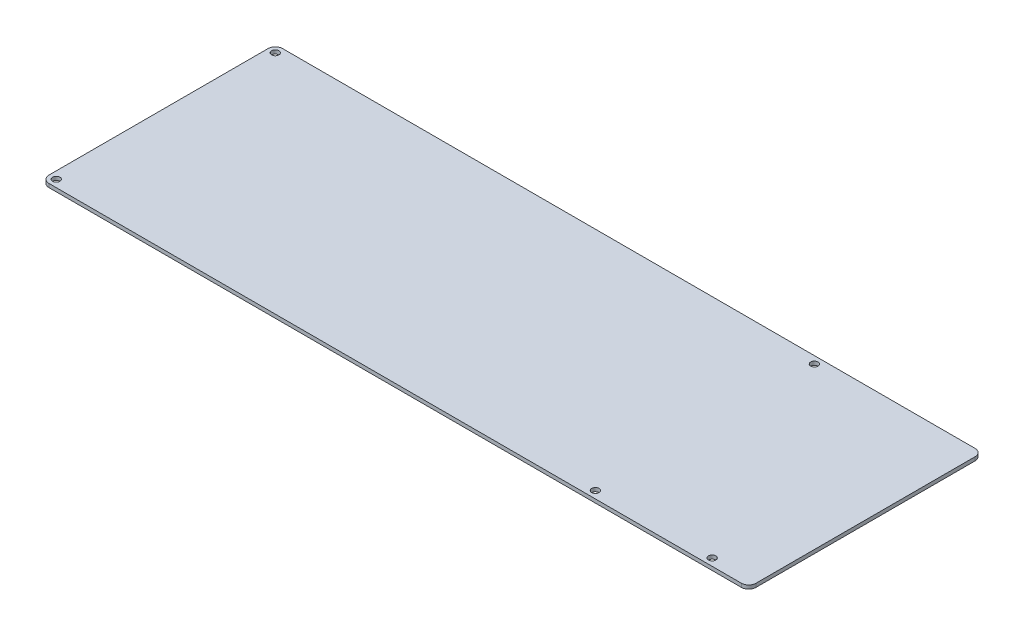
SolidWorks part; units mm, degrees
material "Delrin 2700 NC010, Low Viscosity Acetal Copolymer (SS)"
ref_plane "Front" through (0, 0, 0) normal (0, 0, 1) x (1, 0, 0)
ref_plane "Top" through (0, 0, 0) normal (0, 1, 0) x (1, 0, 0)
ref_plane "Right" through (0, 0, 0) normal (1, 0, 0) x (0, 0, -1)
sketch "Sketch1" plane through (0, 0, 0) normal (0, 1, 0) x (1, 0, 0)
  line L0 (-641.8801, 168.4566) -> (-641.8801, 78.4566) construction
  line L1 (-654.5801, 65.7566) -> (-39.6101, 65.7566)
  line L2 (-654.5801, 65.7566) -> (-654.5801, 268.9566)
  line L3 (-654.5801, 268.9566) -> (-39.6101, 268.9566)
  line L4 (-39.6101, 65.7566) -> (-39.6101, 268.9566)
  line L5 (-641.8801, 78.4566) -> (-541.8801, 78.4566) construction
  line L6 (-377.4301, 256.2566) -> (-192.0101, 256.2566) construction
  line L7 (-52.3101, 97.5066) -> (-52.3101, 237.2066) construction
  line L8 (-648.2301, 262.6066) -> (-45.9601, 262.6066) construction
  line L9 (-45.9601, 72.1066) -> (-45.9601, 262.6066) construction
  line L10 (-648.2301, 72.1066) -> (-45.9601, 72.1066) construction
  line L11 (-648.2301, 72.1066) -> (-648.2301, 262.6066) construction
  line L12 (-179.3101, 268.9566) -> (-179.3101, 65.7566) construction
  line L13 (-141.2101, 237.2066) -> (-141.2101, 97.5066) construction
  circle A0 centre (-648.2301, 262.6066) radius 3.175
  circle A1 centre (-648.2301, 72.1066) radius 3.175
  circle A2 centre (-45.9601, 262.6066) radius 3.175
  circle A3 centre (-45.9601, 72.1066) radius 3.175
  circle A4 centre (-179.3101, 72.1066) radius 3.175
  circle A5 centre (-179.3101, 262.6066) radius 3.175
  circle A6 centre (-77.7101, 72.1066) radius 3.175
  dimension "D6" = 6.35
  dimension "D1" = 12.7
  dimension "D2" = 12.7
  dimension "D3" = 12.7
  dimension "D4" = 12.7
  dimension "D7" = 38.1
  dimension "D8" = 31.75
  dimension "D5" = 6.35
extrude "Boss-Extrude1" add sketch "Sketch1" against normal blind 3.175 contours A3 | L1 L4 L3 L2 A6 A5 A4 A3 A2 A1 A0 | A2
fillet "Fillet1" radius 6.35 4 edges at (-39.6101, -1.5875, -268.9566) (-654.5801, -1.5875, -268.9566) (-39.6101, -1.5875, -65.7566) (-654.5801, -1.5875, -65.7566)
